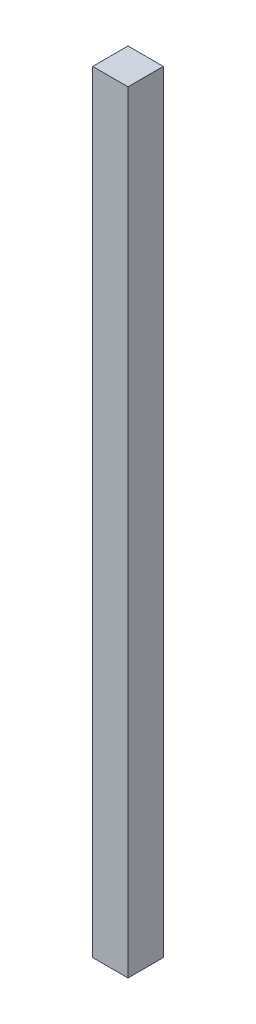
SolidWorks part; units mm, degrees
ref_plane "Front Plane" through (0, 0, 0) normal (0, 0, 1) x (1, 0, 0)
ref_plane "Top Plane" through (0, 0, 0) normal (0, 1, 0) x (1, 0, 0)
ref_plane "Right Plane" through (0, 0, 0) normal (1, 0, 0) x (0, 0, -1)
sketch "Sketch1" plane through (0, 0, 0) normal (0, 1, 0) x (1, 0, 0)
  line L1 (-41.9696, 20.0363) -> (-16.5696, 20.0363)
  line L2 (-41.9696, 20.0363) -> (-41.9696, -5.3637)
  line L3 (-41.9696, -5.3637) -> (-16.5696, -5.3637)
  line L4 (-16.5696, 20.0363) -> (-16.5696, -5.3637)
  dimension "D1" = 25.4
  dimension "D2" = 25.4
extrude "Boss-Extrude1" add sketch "Sketch1" along normal blind 555
